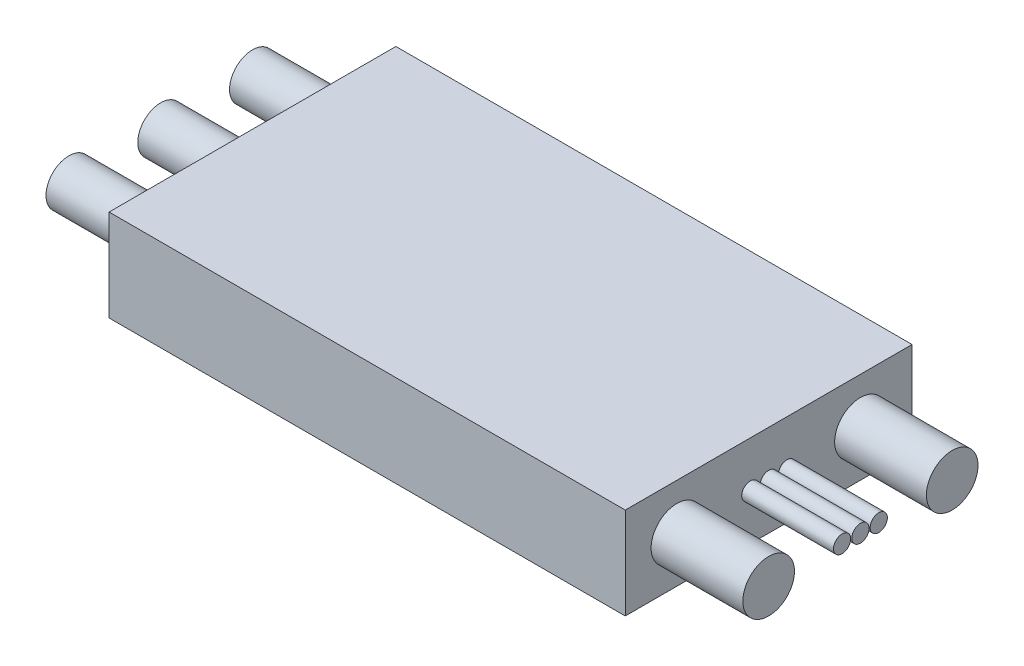
SolidWorks part; units mm, degrees
ref_plane "Front Plane" through (0, 0, 0) normal (0, 0, 1) x (1, 0, 0)
ref_plane "Top Plane" through (0, 0, 0) normal (0, 1, 0) x (1, 0, 0)
ref_plane "Right Plane" through (0, 0, 0) normal (1, 0, 0) x (0, 0, -1)
sketch "Sketch1" plane through (0, 0, 0) normal (0, 1, 0) x (1, 0, 0)
  line L1 (0, 0) -> (45, 0)
  line L2 (0, 0) -> (0, 25)
  line L3 (0, 25) -> (45, 25)
  line L4 (45, 0) -> (45, 25)
  dimension "D1" = 25
  dimension "D2" = 45
extrude "Boss-Extrude1" add sketch "Sketch1" along normal blind 8
sketch "Sketch2" plane through (0, 0, 0) normal (-1, 0, 0) x (0, 0, 1)
  line L0 (-25, 4) -> (0, 4) construction
  line L1 (-25, 8) -> (-25, 0) construction
  line L2 (0, 8) -> (0, 0) construction
  circle A0 centre (-12.5, 4) radius 2
  circle A1 centre (-20.5, 4) radius 2
  circle A2 centre (-4.5, 4) radius 2
  dimension "D3" = 4
  dimension "D1" = 8
  dimension "D2" = 8
extrude "Boss-Extrude2" add sketch "Sketch2" along normal blind 8
sketch "Sketch3" plane through (45, 0, 0) normal (1, 0, 0) x (0, 0, -1)
  line L0 (0, 4) -> (25, 4) construction
  line L1 (0, 8) -> (0, 0) construction
  line L2 (25, 8) -> (25, 0) construction
  circle A0 centre (4.5, 4) radius 2.25
  circle A1 centre (20.5, 4) radius 2.25
  circle A2 centre (10.9, 4) radius 0.75
  circle A3 centre (12.5, 4) radius 0.75
  circle A4 centre (14.1, 4) radius 0.75
  dimension "D2" = 4.5
  dimension "D4" = 1.5
  dimension "D1" = 4.5
  dimension "D3" = 4.5
  dimension "D5" = 1.6
  dimension "D6" = 1.6
extrude "Boss-Extrude5" add sketch "Sketch3" along normal blind 8
